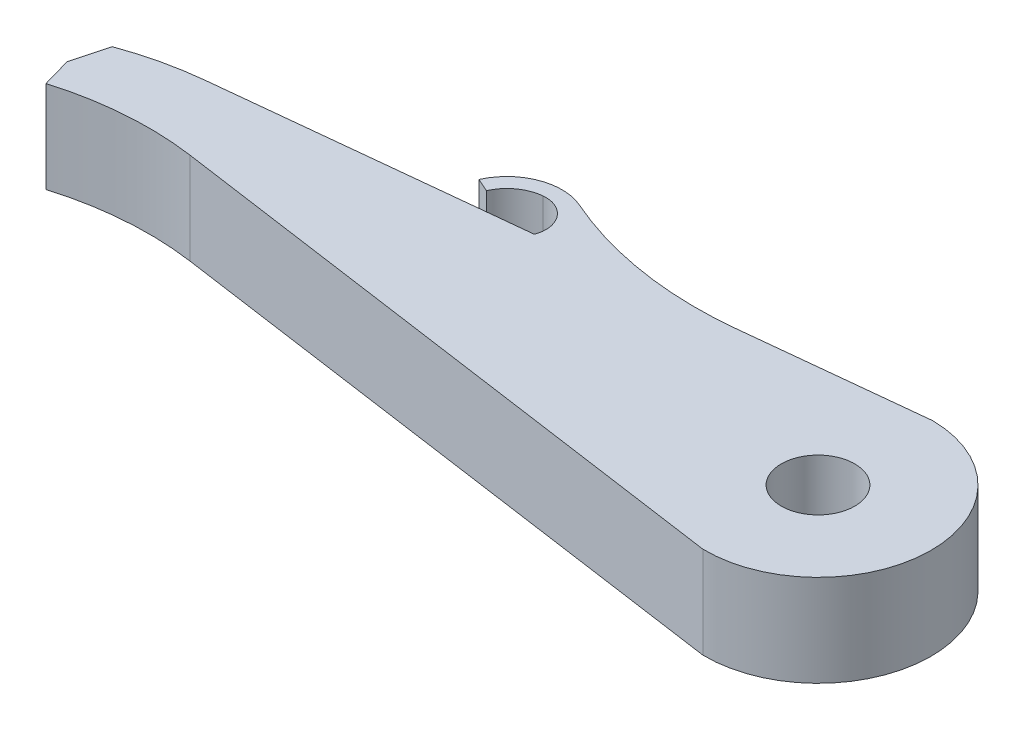
SolidWorks part; units mm, degrees
ref_plane "前视基准面" through (0, 0, 0) normal (0, 0, 1) x (1, 0, 0)
ref_plane "上视基准面" through (0, 0, 0) normal (0, 1, 0) x (1, 0, 0)
ref_plane "右视基准面" through (0, 0, 0) normal (1, 0, 0) x (0, 0, -1)
other "Configuration Table"
sketch "草图2" plane through (0, 0, 0) normal (0, 1, 0) x (1, 0, 0)
  line L0 (0, 0) -> (0, 15) construction
  line L1 (3.3646, 12.557) -> (3.8823, 14.4889) construction
  line L2 (7.5, 12.9904) -> (23.7805, 10.6808)
  line L3 (7.5, 12.9904) -> (8.0176, 14.9222)
  line L4 (3.8823, 14.4889) -> (3.3646, 12.557)
  line L5 (5.9232, 14.9605) -> (23.893, 16.8435)
  line L6 (23.893, 16.8435) -> (23.7805, 10.6808) construction
  line L7 (0, 0) -> (23.8368, 13.7622) construction
  line L8 (23.8497, 16.839) -> (-49703.865, -5194.1491) construction
  line L9 (14.0046, 12.0676) -> (-49490.3467, 7034.8307) construction
  line L10 (23.8368, 13.7622) -> (-1.1572, 14.2185) construction
  line L11 (12.3776, 16.1898) -> (12.0123, 16.3527)
  line L12 (14.8742, 15.8984) -> (14.0584, 15.813)
  arc A0 (0, 13) -> (3.3646, 12.557) centre (0, 0) cw construction
  arc A1 (0, 13) -> (3.8823, 14.4889) centre (4.9145, 5.9915) cw construction
  arc A2 (3.3646, 12.557) -> (7.5, 12.9904) centre (6.2977, 4.5154) cw
  arc A3 (3.8823, 14.4889) -> (8.0176, 14.9222) centre (6.8154, 6.4472) cw
  arc A4 (23.893, 16.8435) -> (23.7805, 10.6808) centre (23.8368, 13.7622) cw
  circle A5 centre (23.8368, 13.7622) radius 1
  arc A6 (14.8742, 15.8984) -> (12.0123, 16.3527) centre (13.3824, 15.7421) ccw
  arc A7 (14.0584, 15.813) -> (13.2678, 16.8361) centre (13.347, 16.0803) ccw
  arc A8 (12.3776, 16.1898) -> (14.4764, 15.8568) centre (13.3824, 15.7421) cw
  point P14 (-1.1572, 14.2185)
  point P21 (15.6403, 11.8356)
  point P31 (0, 0)
  dimension "D5" = 4.2
  dimension "D13" = 2
  dimension "D15" = 150
  dimension "D17" = 1.1
  dimension "D14" = 1.5
  dimension "D1" = 15
  dimension "D2" = 13
  dimension "D3" = 15
  dimension "D4" = 2
  dimension "D7" = 15
  dimension "D8" = 15
  dimension "D9" = 8.5599
  dimension "D10" = 2
  dimension "D11" = 60
  dimension "D12" = 27.5243
  dimension "D16" = 0.34
  dimension "D18" = 0.4
  dimension "D19" = 0.34
  dimension "D20" = 7.5
  dimension "D6" = 2
extrude "凸台-拉伸1" add sketch "草图2" along normal blind 2.5 contours L11 A8 L12 A6 | A8 A7 L5 | A4 L5 L12 A3 L3 L2 A5 | A3 L4 A2 L3
sketch "草图3" plane through (0, 2.5, 0) normal (0, 1, 0) x (1, 0, 0)
  line L0 (3.6235, 13.523) -> (3.8519, 12.7184)
  line L1 (3.8823, 14.4889) -> (3.3646, 12.557) construction
  line L2 (3.8519, 12.7184) -> (3.3646, 12.557)
  line L3 (3.3646, 12.557) -> (3.6235, 13.523)
  arc A0 (7.5, 12.9904) -> (3.3646, 12.557) centre (6.2977, 4.5154) ccw construction
extrude "切除-拉伸1" cut sketch "草图3" against normal blind 10
fillet "圆角1" radius 10 1 edges at (14.8742, 1.25, -15.8984)
